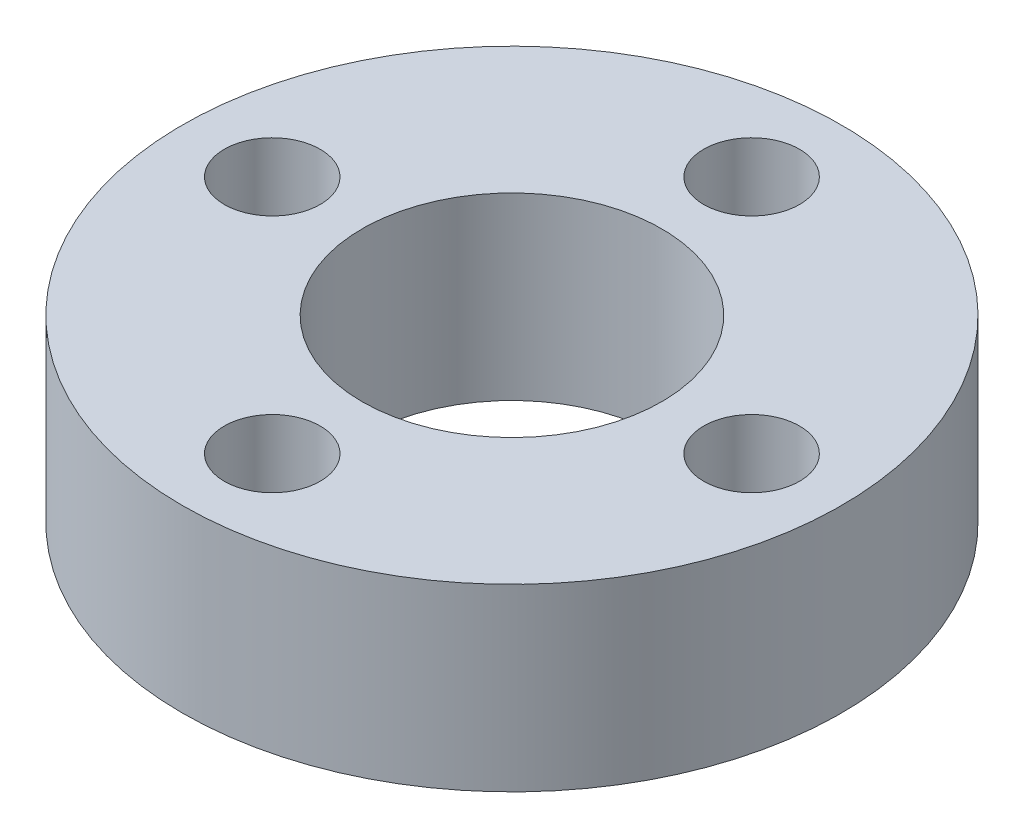
SolidWorks part; units mm, degrees
material "1.0037 (S235JR)"
ref_plane "Front Plane" through (0, 0, 0) normal (0, 0, 1) x (1, 0, 0)
ref_plane "Top Plane" through (0, 0, 0) normal (0, 1, 0) x (1, 0, 0)
ref_plane "Right Plane" through (0, 0, 0) normal (1, 0, 0) x (0, 0, -1)
sketch "Sketch1" plane through (0, 0, 0) normal (0, 1, 0) x (1, 0, 0)
  circle A0 centre (0, 0) radius 27.5
  circle A1 centre (0, 0) radius 20 construction
  circle A2 centre (0, 0) radius 12.5
  circle A3 centre (0, 20) radius 4
  circle A4 centre (20, 0) radius 4
  circle A5 centre (0, -20) radius 4
  circle A6 centre (-20, 0) radius 4
  dimension "D1" = 55
  dimension "D2" = 40
  dimension "D3" = 25
  dimension "D4" = 8
  dimension "D5" = 4
extrude "Boss-Extrude1" add sketch "Sketch1" along normal blind 15
